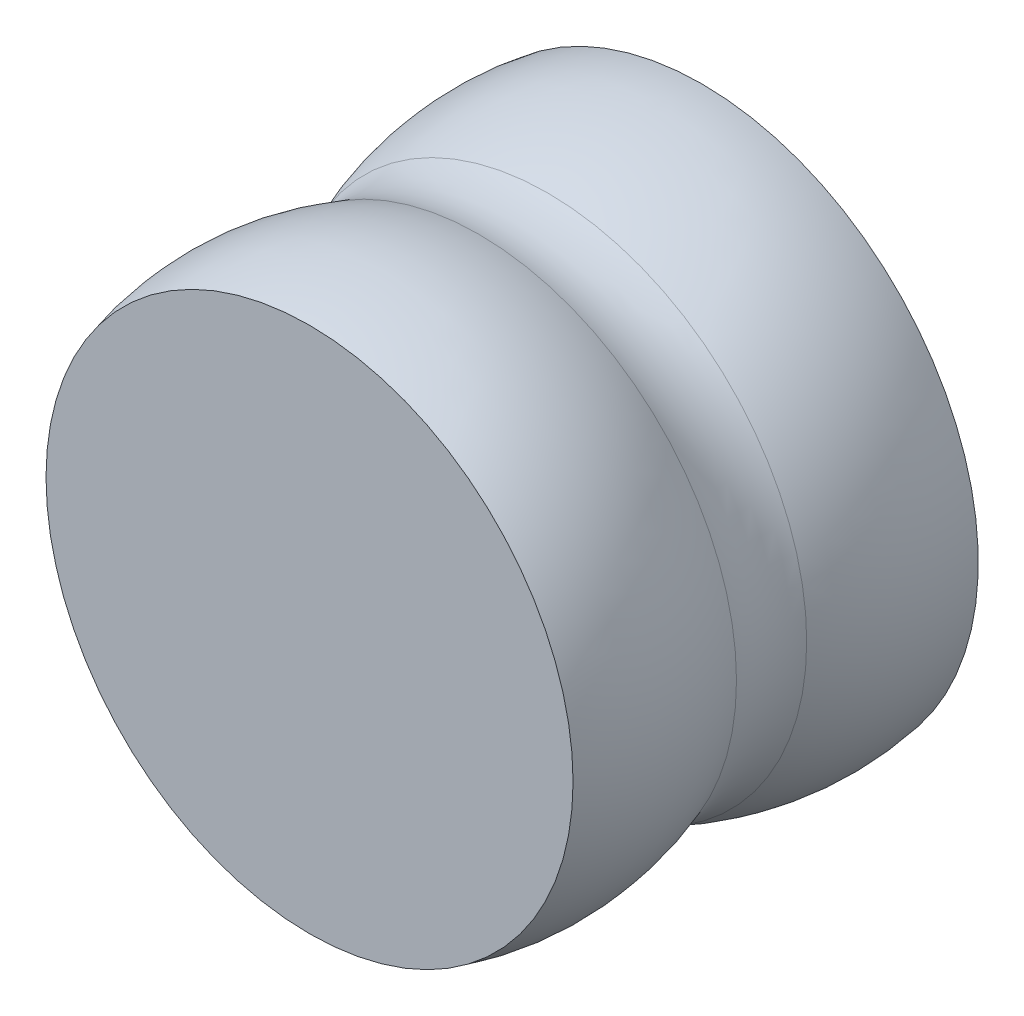
SolidWorks part; units mm, degrees
ref_plane "Front Plane" through (0, 0, 0) normal (0, 0, 1) x (1, 0, 0)
ref_plane "Top Plane" through (0, 0, 0) normal (0, 1, 0) x (1, 0, 0)
ref_plane "Right Plane" through (0, 0, 0) normal (1, 0, 0) x (0, 0, -1)
sketch "Sketch1" plane through (0, 0, 0) normal (1, 0, 0) x (0, 0, -1)
  line L0 (0, 0) -> (-50.9598, 0)
  line L2 (-50.9598, 34.2209) -> (-50.9598, 33.1794)
  line L6 (0, 35.8772) -> (0, 34.8622)
  line L8 (0, 34.8622) -> (0, 0)
  line L9 (-50.9598, 33.1794) -> (-50.9598, 0)
  line L10 (-1.8421, 31.7091) -> (-37.0117, 31.7091) construction
  line L11 (-19.6609, 32.7191) -> (-6.1471, 0) construction
  line L12 (-28.9712, 33.4531) -> (-41.1471, 0) construction
  line L13 (22.9099, 34.8622) -> (-36.6675, 34.8622) construction
  line L14 (-24.752, 31.7091) -> (-24.752, 32.7091) construction
  line L15 (-6.1471, 0) -> (0, 34.8622) construction
  line L16 (-41.1471, 0) -> (-50.9598, 34.2209) construction
  arc A0 (-28.9712, 33.4531) -> (-50.9598, 34.2209) centre (-41.1471, 0) ccw
  arc A1 (-19.6609, 32.7191) -> (0, 34.8622) centre (-6.1471, 0) cw
  arc A2 (-20.0427, 33.6433) -> (0, 35.8772) centre (-6.1471, 0) cw
  arc A3 (-28.9712, 33.4531) -> (-24.752, 32.7091) centre (-24.752, 45.0454) ccw
  arc A4 (-50.9598, 33.1794) -> (-29.3132, 32.5134) centre (-41.1471, 0) cw
  arc A5 (-29.3132, 32.5134) -> (-24.752, 31.7091) centre (-24.752, 45.0454) ccw
  arc A6 (-24.752, 32.7091) -> (-20.0427, 33.6433) centre (-24.752, 45.0454) ccw
  arc A7 (-24.752, 31.7091) -> (-19.6609, 32.7191) centre (-24.752, 45.0454) ccw
  point P9 (0, 0)
  point P10 (-6.1471, 35.4)
revolve "Revolve1" add sketch "Sketch1" angle 360 about L0
equation "\"Nominal_Diameter\"= 35mm"
equation "\"D1@Sketch1\"=\"Nominal_Diameter\" + 0.6mm"
equation "\"Wall_Thickness\"= 1mm"
equation "\"D5@Sketch1\"=\"Wall_Thickness\""
equation "\"D2@Sketch1\"=\"Nominal_Diameter\" + 0.4mm"
equation "\"D3@Sketch1\"=\"Nominal_Diameter\""
